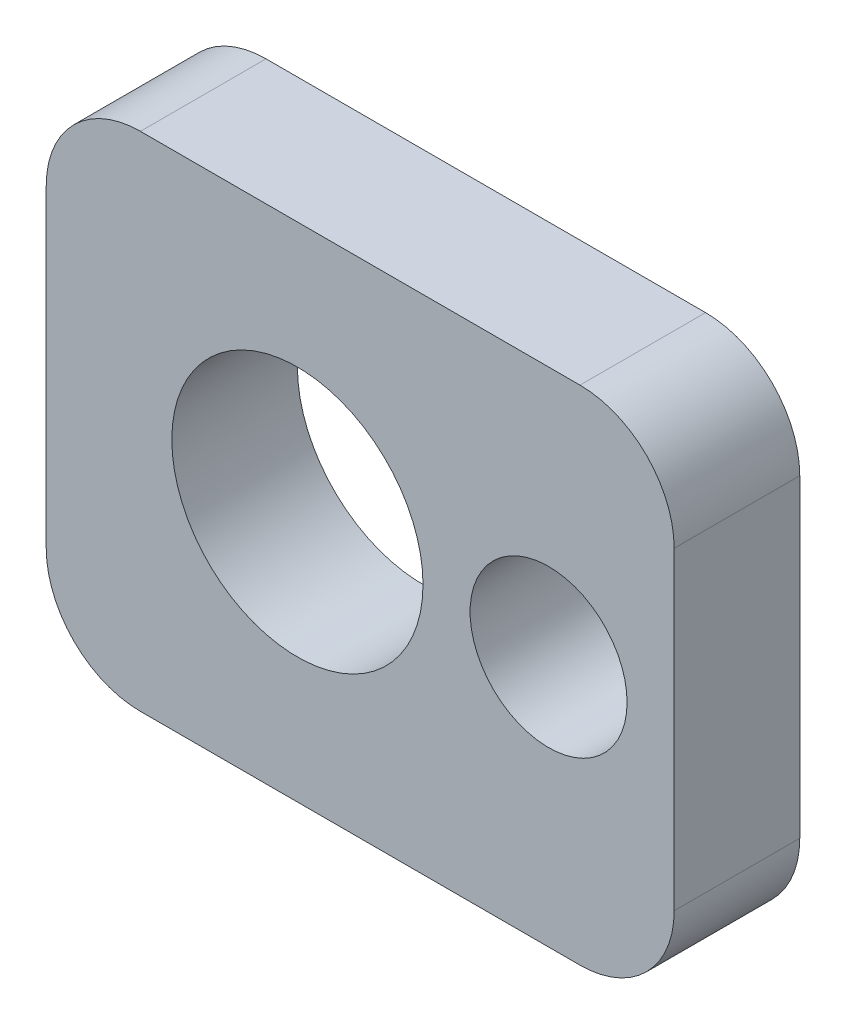
SolidWorks part; units mm, degrees
ref_plane "Front Plane" through (0, 0, 0) normal (0, 0, 1) x (1, 0, 0)
ref_plane "Top Plane" through (0, 0, 0) normal (0, 1, 0) x (1, 0, 0)
ref_plane "Right Plane" through (0, 0, 0) normal (1, 0, 0) x (0, 0, -1)
sketch "Sketch1" plane through (0, 0, 0) normal (0, 0, 1) x (1, 0, 0)
  line L1 (35, -40) -> (-35, -40)
  line L2 (50, -25) -> (50, 25)
  line L3 (35, 40) -> (-35, 40)
  line L4 (-50, -25) -> (-50, 25)
  line L5 (50, -40) -> (-50, 40) construction
  line L6 (50, 40) -> (-50, -40) construction
  arc A0 (-35, -40) -> (-50, -25) centre (-35, -25) cw
  arc A1 (35, -40) -> (50, -25) centre (35, -25) ccw
  arc A2 (50, 25) -> (35, 40) centre (35, 25) ccw
  arc A3 (-50, 25) -> (-35, 40) centre (-35, 25) cw
  point P0 (0, 0)
  dimension "D1" = 15
  dimension "D2" = 70
  dimension "D3" = 50
extrude "Boss-Extrude1" add sketch "Sketch1" along normal blind 20
sketch "Sketch3" plane through (0, 0, 20) normal (0, 0, 1) x (1, 0, 0)
  line L0 (-50, 25) -> (-50, -25) construction
  circle A0 centre (-10, 0) radius 20
  point P4 (-50, 0)
  dimension "D1" = 40
  dimension "D2" = 40
extrude "Cut-Extrude2" cut sketch "Sketch3" against normal through all and the other way through all
sketch "Sketch4" plane through (0, 0, 20) normal (0, 0, 1) x (1, 0, 0)
  circle A0 centre (30, 0) radius 12.5
  circle A1 centre (-10, 0) radius 20 construction
  dimension "D1" = 25
  dimension "D2" = 40
extrude "Cut-Extrude3" cut sketch "Sketch4" against normal through all
